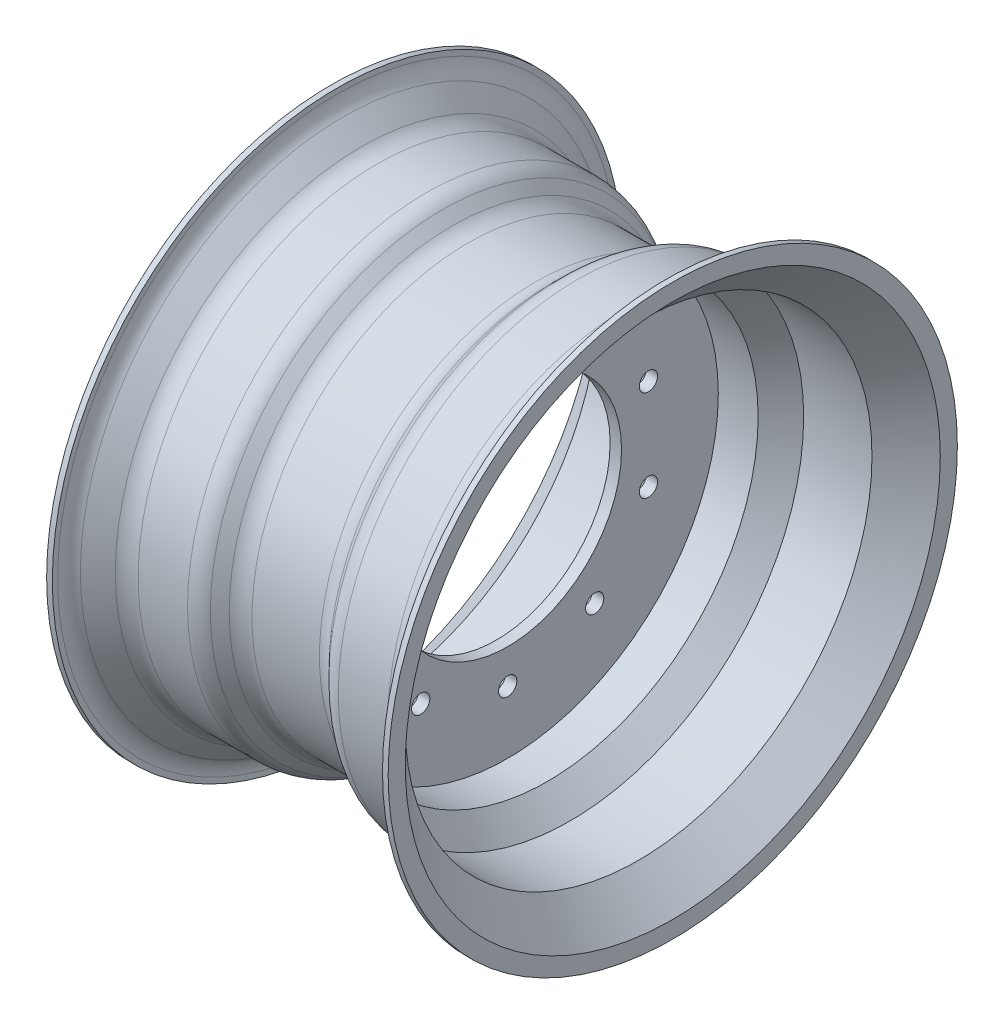
SolidWorks part; units mm, degrees
ref_plane "Front Plane" through (0, 0, 0) normal (0, 0, 1) x (1, 0, 0)
ref_plane "Top Plane" through (0, 0, 0) normal (0, 1, 0) x (1, 0, 0)
ref_plane "Right Plane" through (0, 0, 0) normal (1, 0, 0) x (0, 0, -1)
sketch "Sketch1" plane through (0, 0, 0) normal (0, 0, 1) x (1, 0, 0)
  line L0 (0, 226.816) -> (0, 0) construction
  line L1 (0, 0) -> (-347.1819, 0) construction
  line L2 (-150, 250) -> (-150, 235)
  line L3 (-150, 235) -> (-120, 205)
  line L4 (-120, 205) -> (-60, 205)
  line L5 (-60, 205) -> (-40, 185)
  line L6 (-40, 185) -> (-5, 185)
  line L7 (60, 205) -> (40, 185)
  line L8 (120, 205) -> (60, 205)
  line L9 (150, 235) -> (120, 205)
  line L10 (150, 250) -> (150, 235)
  line L11 (-145, 250) -> (-145, 237.0711)
  line L12 (-145, 237.0711) -> (-117.9289, 210)
  line L13 (-117.9289, 210) -> (-57.9289, 210)
  line L14 (-57.9289, 210) -> (-37.9289, 190)
  line L15 (-37.9289, 190) -> (37.9289, 190)
  line L16 (57.9289, 210) -> (37.9289, 190)
  line L17 (117.9289, 210) -> (57.9289, 210)
  line L18 (145, 237.0711) -> (117.9289, 210)
  line L19 (145, 250) -> (145, 237.0711)
  line L20 (-150, 250) -> (-145, 250)
  line L21 (145, 250) -> (150, 250)
  line L22 (-40, 185) -> (40, 185) construction
  line L24 (-5, 185) -> (-5, 100)
  line L25 (-5, 100) -> (5, 100)
  line L26 (5, 185) -> (5, 100)
  line L27 (5, 185) -> (40, 185)
  point P11 (0, 185)
  dimension "D1" = 250
  dimension "D2" = 15
  dimension "D3" = 30
  dimension "D4" = 60
  dimension "D5" = 20
  dimension "D6" = 40
  dimension "D7" = 135
  dimension "D8" = 135
  dimension "D10" = 10
  dimension "D11" = 5
  dimension "D12" = 100
  dimension "D9" = 5
revolve "Revolve1" add sketch "Sketch1" angle 360 about L1
fillet "Fillet1" radius 20 8 edges at (145, 0, -237.0711) (117.9289, 0, -210) (57.9289, 0, -210) (37.9289, 0, -190) (-37.9289, 0, -190) (-57.9289, 0, -210) (-117.9289, 0, -210) (-145, 0, -237.0711)
sketch "Sketch2" plane through (5, 0, 0) normal (1, 0, 0) x (0, 0, -1)
  circle A0 centre (0, 130) radius 8
  point P2 (0, 0)
  dimension "D1" = 16
  dimension "D2" = 130
extrude "Cut-Extrude1" cut sketch "Sketch2" against normal blind 10
pattern_circular "CirPattern1" count 10 over 360 about axis through (0, 0, 0) along (1, 0, 0) of "Cut-Extrude1"
